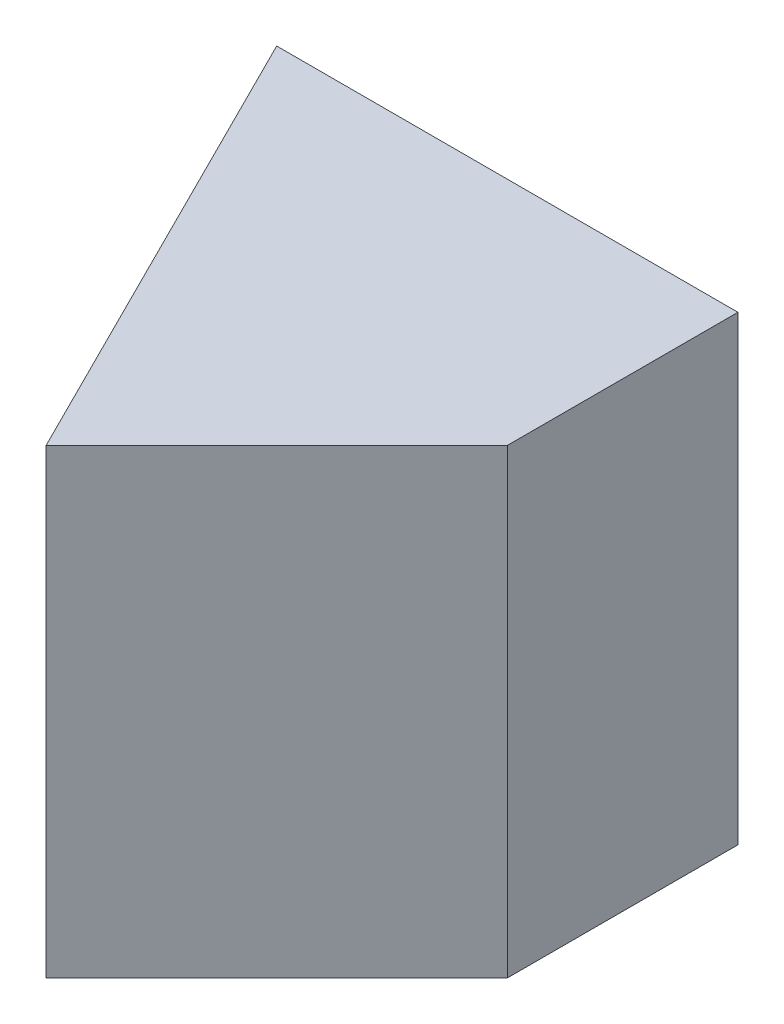
SolidWorks part; units mm, degrees
ref_plane "Front Plane" through (0, 0, 0) normal (0, 0, 1) x (1, 0, 0)
ref_plane "Top Plane" through (0, 0, 0) normal (0, 1, 0) x (1, 0, 0)
ref_plane "Right Plane" through (0, 0, 0) normal (1, 0, 0) x (0, 0, -1)
sketch "Sketch1" plane through (0, 0, 0) normal (0, 0, 1) x (1, 0, 0)
  line L1 (0, 0) -> (20, 0)
  line L2 (0, 0) -> (0, 20)
  line L3 (0, 20) -> (20, 20)
  line L4 (20, 0) -> (20, 20)
  dimension "D1" = 20
  dimension "D2" = 20
extrude "Boss-Extrude1" add sketch "Sketch1" along normal blind 20
sketch "Sketch2" plane through (0, 20, 0) normal (0, 1, 0) x (1, 0, 0)
  line L0 (0, 0) -> (10, -20)
  line L1 (20, -20) -> (0, -20) construction
  line L2 (10, -20) -> (0, -20)
  line L3 (0, -20) -> (0, 0)
extrude "Cut-Extrude1" cut sketch "Sketch2" against normal blind 20
sketch "Sketch3" plane through (0, 20, 0) normal (0, 1, 0) x (1, 0, 0)
  line L0 (20, -20) -> (20, -10)
  line L1 (20, -20) -> (20, 0) construction
  line L2 (20, -10) -> (10, -20)
  line L3 (10, -20) -> (20, -20)
extrude "Cut-Extrude2" cut sketch "Sketch3" against normal blind 20
